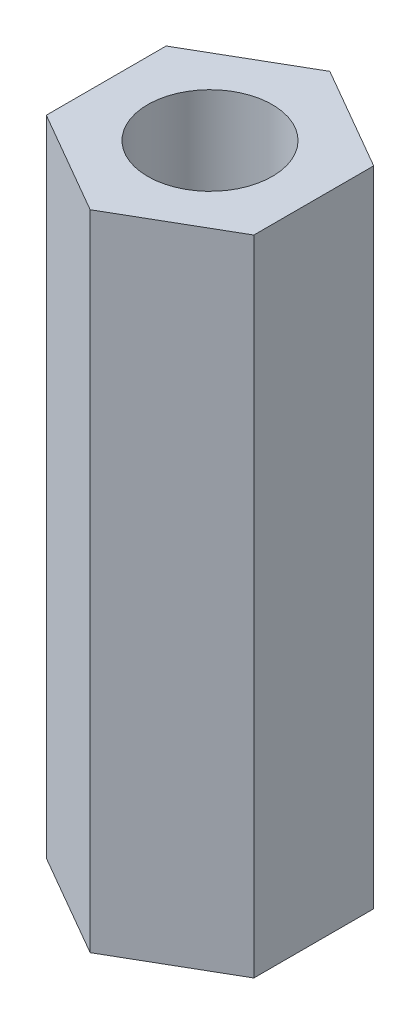
SolidWorks part; units mm, degrees
ref_plane "前基準面" through (0, 0, 0) normal (0, 0, 1) x (1, 0, 0)
ref_plane "上基準面" through (0, 0, 0) normal (0, 1, 0) x (1, 0, 0)
ref_plane "右基準面" through (0, 0, 0) normal (1, 0, 0) x (0, 0, -1)
sketch "草圖1" plane through (0, 0, 0) normal (0, 1, 0) x (1, 0, 0)
  line L0 (0, -5.1664) -> (0, 5.1664) construction
  line L1 (0, 2.8868) -> (-2.5, 1.4434)
  line L2 (-2.5, 1.4434) -> (-2.5, -1.4434)
  line L3 (-2.5, -1.4434) -> (0, -2.8868)
  line L4 (0, -2.8868) -> (2.5, -1.4434)
  line L5 (2.5, -1.4434) -> (2.5, 1.4434)
  line L6 (2.5, 1.4434) -> (0, 2.8868)
  circle A0 centre (0, 0) radius 1.5
  circle A1 centre (0, 0) radius 2.5 construction
  point P16 (0, 0)
  dimension "D1" = 3
  dimension "D2" = 5
extrude "填料-伸長1" add sketch "草圖1" along normal blind 15.5
